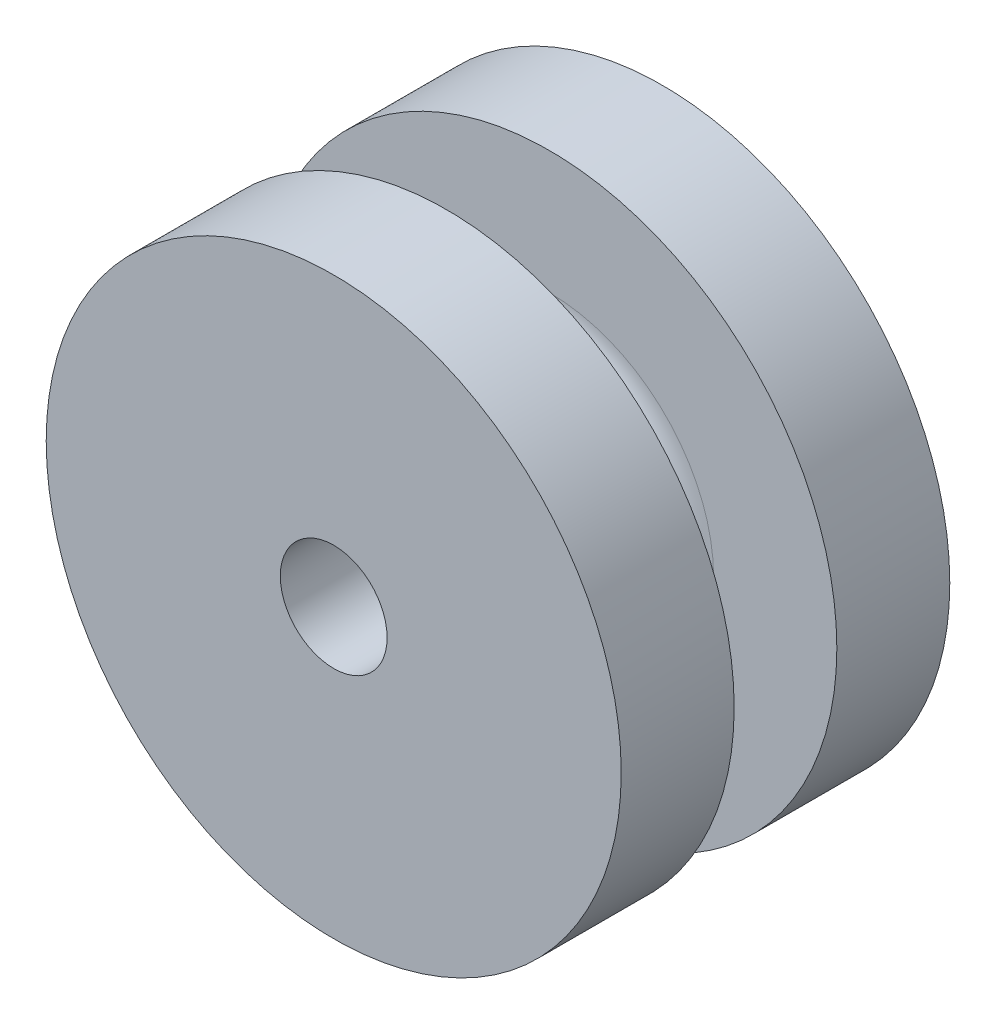
SolidWorks part; units mm, degrees
ref_plane "Plan de face" through (0, 0, 0) normal (0, 0, 1) x (1, 0, 0)
ref_plane "Plan de dessus" through (0, 0, 0) normal (0, 1, 0) x (1, 0, 0)
ref_plane "Plan de droite" through (0, 0, 0) normal (1, 0, 0) x (0, 0, -1)
sketch "Esquisse1" plane through (0, 0, 0) normal (0, 0, 1) x (1, 0, 0)
  circle A0 centre (0, 0) radius 7
  dimension "D1" = 14
extrude "Boss.-Extru.1" add sketch "Esquisse1" along normal blind 8
ref_plane "Plan1" through (0, 0, 4) normal (0, 0, -1) x (-1, 0, 0)
sketch "Esquisse2" plane through (0, 0, 4) normal (0, 0, -1) x (-1, 0, 0)
  circle A0 centre (0, 0) radius 7
  circle A1 centre (0, 0) radius 7 construction
  circle A2 centre (0, 0) radius 3
  dimension "D1" = 4
extrude "Enlèv. mat.-Extru.2" cut sketch "Esquisse2" against normal blind 1.25 and the other way blind 1.25
fillet "Congé1" radius 1 2 edges at (-3, 0, 2.75) (-3, 0, 5.25)
sketch "Esquisse3" plane through (0, 0, 0) normal (0, 0, -1) x (-1, 0, 0)
  circle A0 centre (0, 0) radius 1.3
  dimension "D1" = 2.6
extrude "Enlèv. mat.-Extru.3" cut sketch "Esquisse3" against normal up to next
